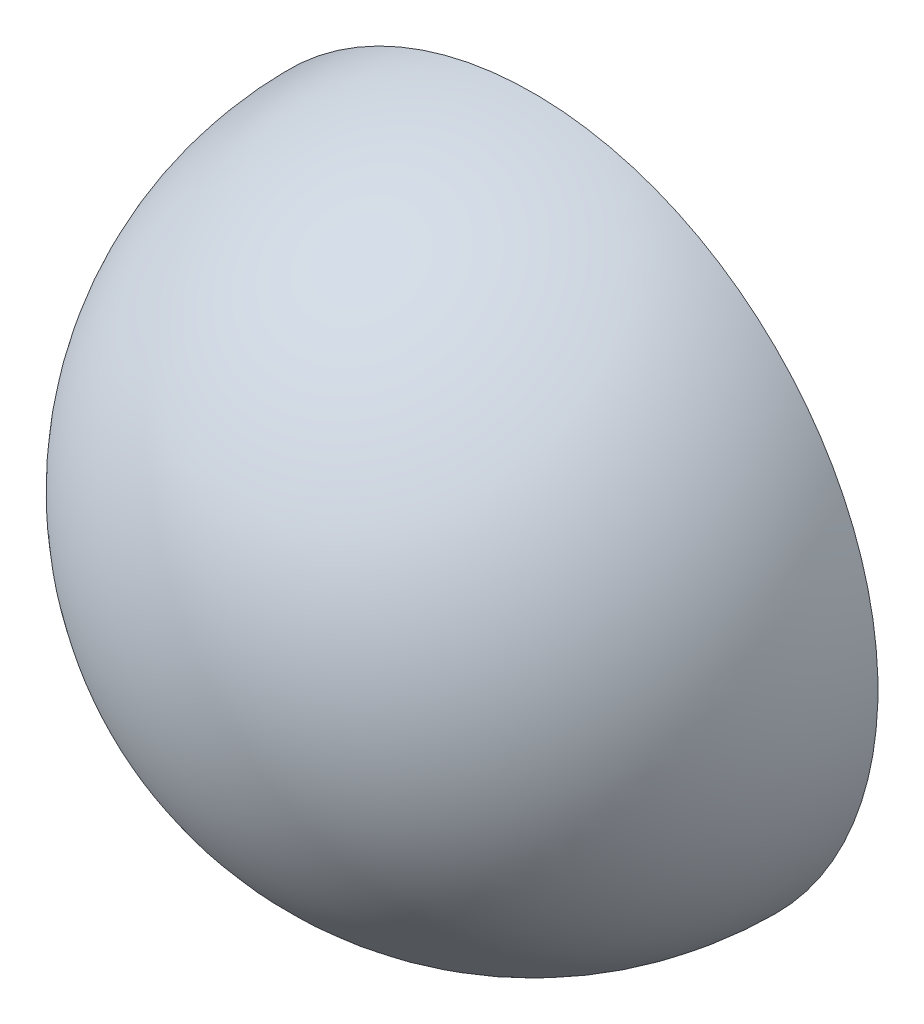
SolidWorks part; units mm, degrees
ref_plane "Front Plane" through (0, 0, 0) normal (0, 0, 1) x (1, 0, 0)
ref_plane "Top Plane" through (0, 0, 0) normal (0, 1, 0) x (1, 0, 0)
ref_plane "Right Plane" through (0, 0, 0) normal (1, 0, 0) x (0, 0, -1)
sketch "Sketch1" plane through (0, 0, 0) normal (0, 0, 1) x (1, 0, 0)
  line L1 (-100, 0) -> (-98, 0)
  line L3 (-2, 0) -> (0, 0)
  line L4 (-98, 0) -> (-2, 0) construction
  arc A0 (-100, 0) -> (0, 0) centre (-50, 0) cw
  arc A1 (-98, 0) -> (-2, 0) centre (-50, 0) cw
  dimension "D1" = 100
  dimension "D2" = 2
revolve "Revolve1" add sketch "Sketch1" angle 180 about L4
